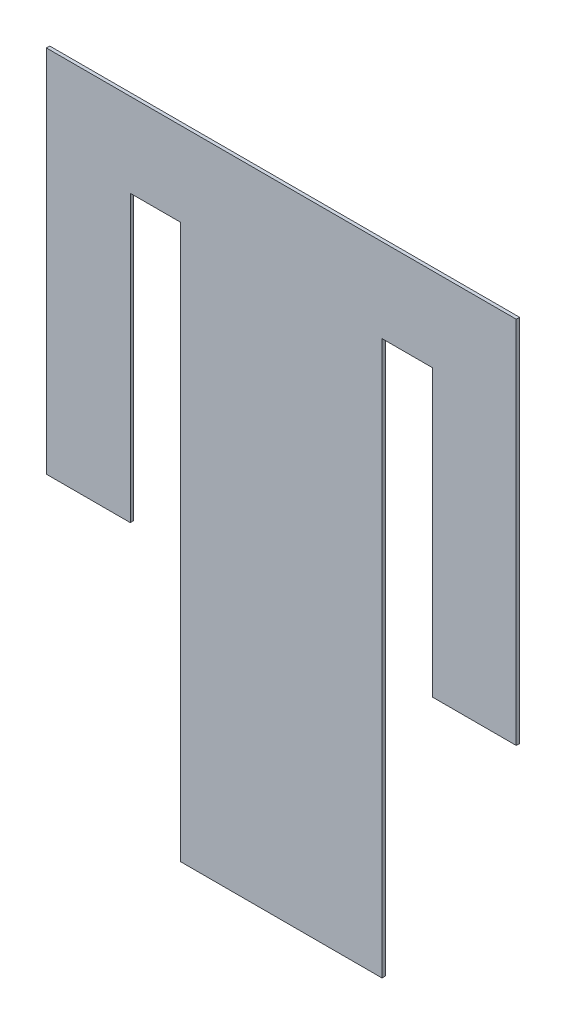
SolidWorks part; units mm, degrees
ref_plane "Front Plane" through (0, 0, 0) normal (0, 0, 1) x (1, 0, 0)
ref_plane "Top Plane" through (0, 0, 0) normal (0, 1, 0) x (1, 0, 0)
ref_plane "Right Plane" through (0, 0, 0) normal (1, 0, 0) x (0, 0, -1)
sketch "Sketch1" plane through (0, 0, 0) normal (0, 0, 1) x (1, 0, 0)
  line L0 (0, 0) -> (0, 220)
  line L5 (0, 220) -> (280, 220)
  line L6 (280, 220) -> (280, 0)
  line L11 (280, 0) -> (230, 0)
  line L12 (230, 0) -> (230, 170)
  line L13 (230, 170) -> (200, 170)
  line L14 (200, 170) -> (200, -160)
  line L15 (200, -160) -> (80, -160)
  line L16 (80, -160) -> (80, 170)
  line L17 (80, 170) -> (50, 170)
  line L18 (50, 170) -> (50, 0)
  line L19 (50, 0) -> (0, 0)
  dimension "D1" = 280
  dimension "D2" = 220
  dimension "D3" = 120
  dimension "D4" = 30
  dimension "D6" = 50
  dimension "D8" = 330
  dimension "15" = 170
extrude "Boss-Extrude1" add sketch "Sketch1" along normal blind 2
